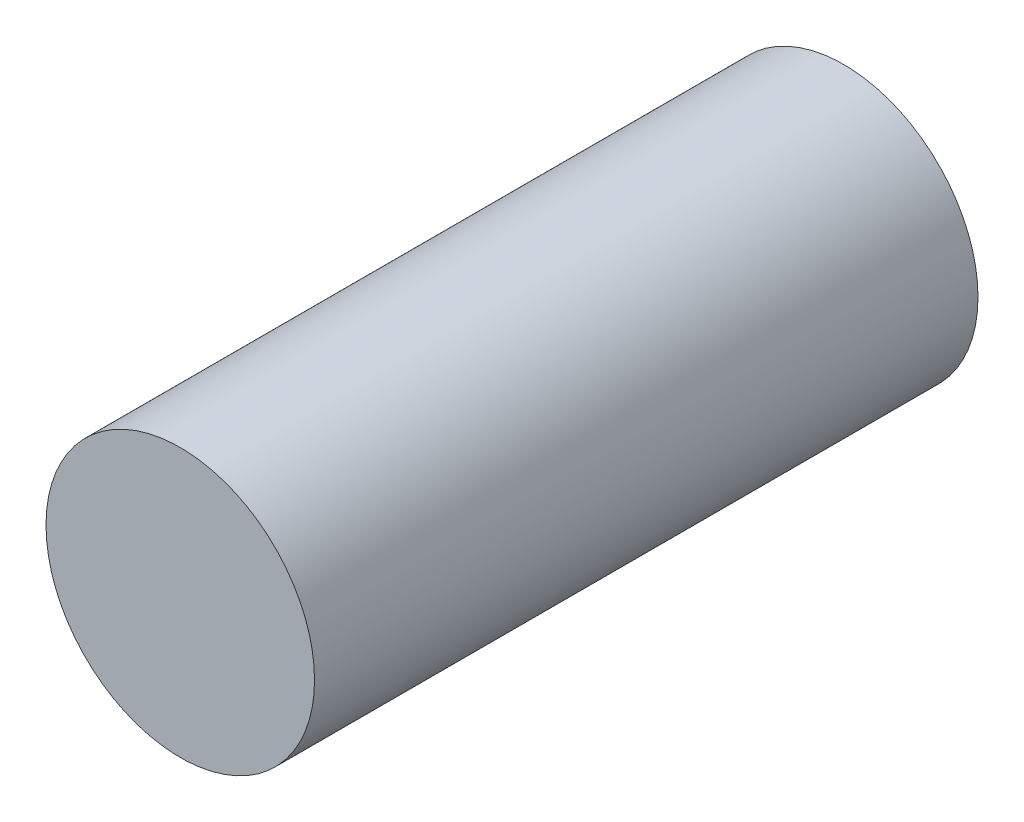
SolidWorks part; units mm, degrees
ref_plane "Front" through (0, 0, 0) normal (0, 0, 1) x (1, 0, 0)
ref_plane "Top" through (0, 0, 0) normal (0, 1, 0) x (1, 0, 0)
ref_plane "Right" through (0, 0, 0) normal (1, 0, 0) x (0, 0, -1)
sketch "Sketch1" plane through (0, 0, 0) normal (0, 0, 1) x (1, 0, 0)
  circle A0 centre (0, 0) radius 8.5
  dimension "D1" = 17
extrude "Boss-Extrude1" add sketch "Sketch1" along normal blind 42
